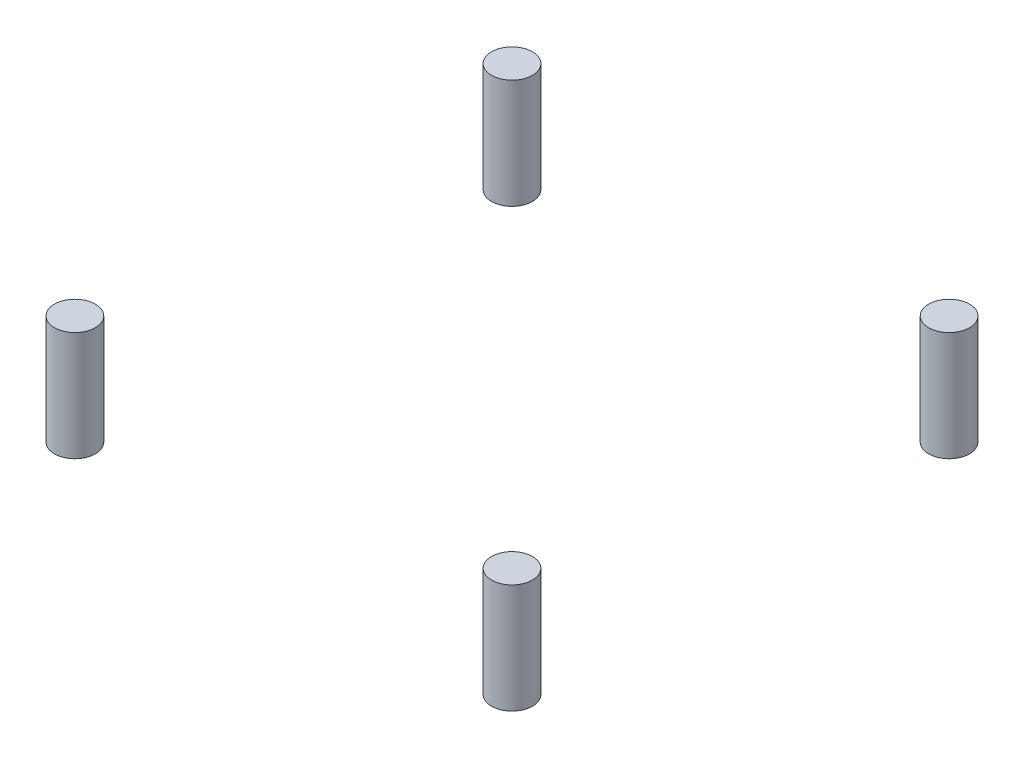
SolidWorks part; units mm, degrees
ref_plane "Front Plane" through (0, 0, 0) normal (0, 0, 1) x (1, 0, 0)
ref_plane "Top Plane" through (0, 0, 0) normal (0, 1, 0) x (1, 0, 0)
ref_plane "Right Plane" through (0, 0, 0) normal (1, 0, 0) x (0, 0, -1)
sketch "Sketch1" plane through (0, 0, 0) normal (0, 1, 0) x (1, 0, 0)
  line L0 (0, 0) -> (0, 38.3357) construction
  line L1 (0, 0) -> (-54.8976, 0) construction
  line L2 (-33.2004, 33.2004) -> (0, 0) construction
  circle A0 centre (-33.2004, 33.2004) radius 3.1044
  circle A1 centre (33.2004, 33.2004) radius 3.1044
  circle A2 centre (33.2004, -33.2004) radius 3.1044
  circle A3 centre (-33.2004, -33.2004) radius 3.1044
  point P8 (0, 0)
  point P16 (0, 0)
  dimension "D3" = 6.2088
  dimension "D1" = 45
  dimension "D2" = 46.9524
  dimension "D4" = 4
extrude "Boss-Extrude1" add sketch "Sketch1" along normal blind 16.6
